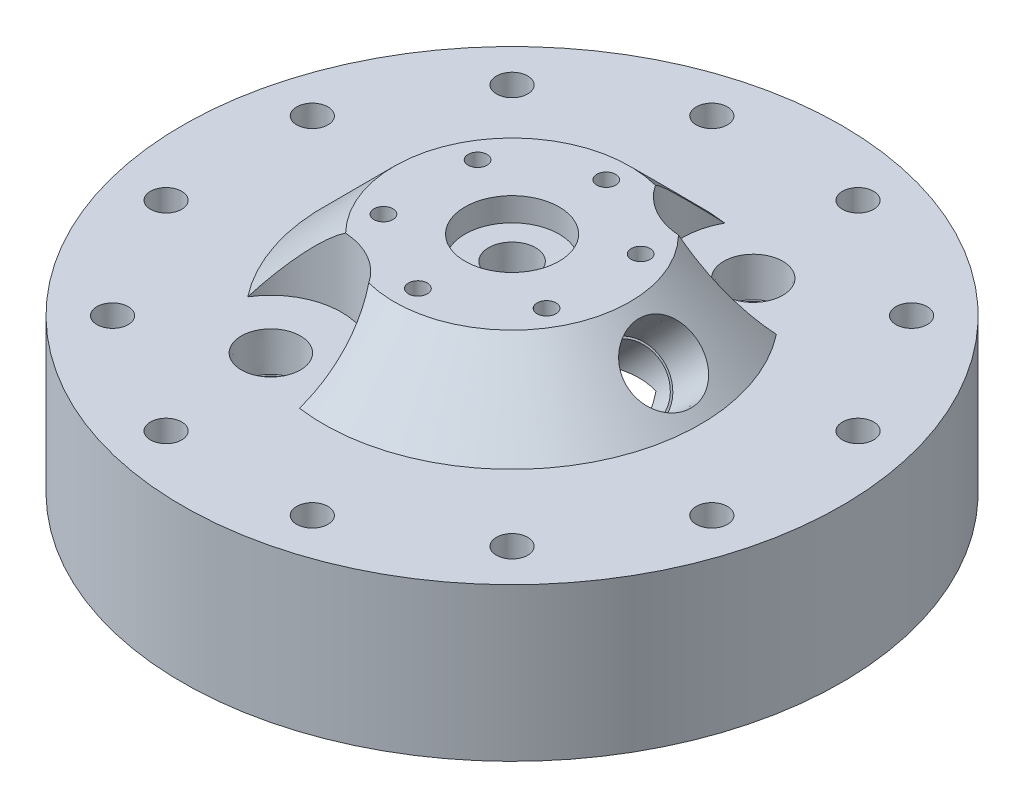
SolidWorks part; units mm, degrees
ref_plane "Front Plane" through (0, 0, 0) normal (0, 0, 1) x (1, 0, 0)
ref_plane "Top Plane" through (0, 0, 0) normal (0, 1, 0) x (1, 0, 0)
ref_plane "Right Plane" through (0, 0, 0) normal (1, 0, 0) x (0, 0, -1)
sketch "Sketch1" plane through (0, 0, 0) normal (0, 0, 1) x (1, 0, 0)
  line L0 (0, 0) -> (0, 51.199) construction
  line L2 (-88.9, 0) -> (-88.9, 41.275)
  line L3 (-88.9, 41.275) -> (-50.8, 41.275)
  line L4 (-50.8, 41.275) -> (-31.75, 60.325)
  line L5 (-31.75, 60.325) -> (-12.7, 60.325)
  line L6 (0, 53.975) -> (0, 34.925)
  line L8 (-31.75, 34.925) -> (0, 34.925)
  line L12 (-31.75, 34.925) -> (-31.75, 22.225)
  line L15 (-31.75, 22.225) -> (-50.8, 22.225)
  line L16 (-50.8, 22.225) -> (-50.8, 3.175)
  line L17 (-50.8, 3.175) -> (-52.3875, 3.175)
  line L18 (-52.3875, 3.175) -> (-52.3875, 5.715)
  line L19 (-52.3875, 5.715) -> (-55.9435, 5.715)
  line L20 (-55.9435, 5.715) -> (-55.9435, 3.175)
  line L21 (-88.9, 0) -> (-57.15, 0)
  line L23 (-55.9435, 3.175) -> (-57.15, 3.175)
  line L24 (-57.15, 3.175) -> (-57.15, 0)
  line L25 (-12.7, 60.325) -> (-12.7, 53.975)
  line L26 (-12.7, 53.975) -> (0, 53.975)
  point P8 (0, 56.7401)
  dimension "D1" = 6.35
  dimension "D2" = 31.75
  dimension "D3" = 19.05
  dimension "D4" = 31.75
  dimension "D5" = 88.9
  dimension "D6" = 12.7
  dimension "D7" = 135
  dimension "D8" = 3.175
  dimension "D9" = 22.225
  dimension "D10" = 41.275
  dimension "D11" = 6.35
  dimension "D12" = 50.8
  dimension "D13" = 3.556
  dimension "D14" = 2.54
  dimension "D15" = 1.5875
  dimension "D16" = 6.35
  dimension "D17" = 12.7
revolve "Revolve1" add sketch "Sketch1" angle 360 about L0
hole_wizard "5/16 Clearance Hole1" positions "Sketch4" profile "Sketch6" hole size "5/16" standard "ANSI Inch" end condition through all
sketch "Sketch4" plane through (0, 41.275, 0) normal (0, 1, 0) x (1, 0, 0)
  line L0 (-73.6035, -19.722) -> (0, 0) construction
  line L2 (0, 0) -> (-63.9148, 0) construction
  point P0 (-73.6035, -19.722)
  dimension "D1" = 76.2
  dimension "D2" = 15
sketch "Sketch6" plane through (-73.6035, 41.275, 19.722) normal (1, 0, 0) x (0, 0, 1)
  line L0 (0, 0) -> (0, 41.275)
  line L1 (0, 41.275) -> (4.2164, 41.275)
  line L2 (4.2164, 41.275) -> (4.2164, 0)
  line L5 (4.2164, 0) -> (0, 0)
  line L11 (0, -6.35) -> (0, 107.95) construction
  dimension "Thru Hole Dia." = 8.4328
  dimension "Thru Hole Depth" = 41.275
pattern_circular "CirPattern1" count 12 over 360 about axis through (0, 0, 0) along (0, 1, 0) of "5/16 Clearance Hole1"
hole_wizard "1/2 (0.5) Diameter Hole1" positions "Sketch7" profile "Sketch8" hole size "1/2" standard "ANSI Inch" end condition through all
sketch "Sketch7" plane through (0, 60.325, 0) normal (0, 1, 0) x (1, 0, 0)
  point P0 (0, 0)
sketch "Sketch8" plane through (0, 60.325, 0) normal (1, 0, 0) x (0, 0, 1)
  line L0 (0, 0) -> (0, 60.325)
  line L1 (0, 60.325) -> (6.35, 60.325)
  line L2 (6.35, 60.325) -> (6.35, 0)
  line L5 (6.35, 0) -> (0, 0)
  line L11 (0, -6.35) -> (0, 107.95) construction
  dimension "Thru Hole Dia." = 12.7
  dimension "Thru Hole Depth" = 60.325
ref_plane "Plane1" through (46.0375, 46.0375, 0) normal (0.7071, 0.7071, 0) x (0, 0, -1)
sketch "Sketch9" plane through (46.0375, 46.0375, 0) normal (0.7071, 0.7071, 0) x (0, 0, -1)
  line L0 (0, -6.7352) -> (0, 20.2056) construction
  ellipse E0 centre (0, 29.1858) end of major axis (-50.8, 29.1858) minor radius 35.921 construction
  ellipse E1 centre (0, 42.6562) end of major axis (-31.75, 42.6562) minor radius 22.4506 construction
  point P15 (0, 6.7352)
hole_wizard "1/2 NPT Tapped Hole1" positions "Sketch10" profile "Sketch11" size "1/2" standard "ANSI Inch" end condition through all
sketch "Sketch10" plane through (46.0375, 46.0375, 0) normal (0.7071, 0.7071, 0) x (0, 0, -1)
  point P0 (0, 6.7352)
sketch "Sketch11" plane through (41.275, 50.8, 0) normal (0, 0, 1) x (-0.7071, 0.7071, 0)
  line L0 (0, 0) -> (0, 127.9686)
  line L1 (0, 127.9686) -> (8.9281, 127.9686)
  line L2 (-9.4797, 13.462) -> (-9.8828, 0) construction
  line L3 (8.9281, 127.9686) -> (8.9281, 13.462)
  line L4 (8.9281, 13.462) -> (9.4797, 13.462)
  line L5 (9.4797, 13.462) -> (9.8828, 0)
  line L7 (9.8828, 0) -> (0, 0)
  line L8 (0, -6.35) -> (0, 107.95) construction
  line L11 (-8.9281, 13.462) -> (-9.4797, 13.462) construction
  dimension "Thru Tap Drill Dia." = 17.8562
  dimension "Thru Tap Drill Depth" = 127.9686
  dimension "Thread Dia." = 19.7656
  dimension "Thread Angle" = 3.43
  dimension "Thread Depth" = 13.462
cosmetic thread "Hole Thread3" parameters "D1"=13.462, "D2"=36.8399
hole_wizard "1 (1.5) Diameter Hole1" positions "Sketch14" profile "Sketch16" hole size "1" standard "ANSI Inch"
sketch "Sketch14" plane through (0, 60.325, 0) normal (0, 1, 0) x (1, 0, 0)
  line L0 (-23.8125, -41.2445) -> (0, 0) construction
  line L2 (0, 0) -> (-62.2091, 0) construction
  point P0 (-23.8125, -41.2445)
  dimension "D1" = 47.625
  dimension "D2" = 60
sketch "Sketch16" plane through (-23.8125, 60.325, 41.2445) normal (1, 0, 0) x (0, 0, 1)
  line L0 (0, 0) -> (0, 30.4964)
  line L1 (0, 30.4964) -> (19.05, 19.05)
  line L2 (19.05, 19.05) -> (19.05, 0)
  line L5 (19.05, 0) -> (0, 0)
  line L10 (0, 30.4964) -> (-19.05, 19.05) construction
  line L11 (0, -6.35) -> (0, 107.95) construction
  dimension "Hole Dia." = 38.1
  dimension "Hole Depth" = 19.05
  dimension "Drill Angle" = 118
hole_wizard "3/8 NPT Tapped Hole1" positions "Sketch17" profile "Sketch19" size "3/8" standard "ANSI Inch"
sketch "Sketch17" plane through (0, 41.275, 0) normal (0, 1, 0) x (1, 0, 0)
  line L0 (0, 0) -> (-55.2485, 0) construction
  line L2 (0, 0) -> (-23.8125, -41.2445) construction
  point P0 (-23.8125, -41.2445)
  dimension "D1" = 47.625
  dimension "D2" = 60
cosmetic thread "Hole Thread4" parameters "D1"=10.414, "D2"=17.1495
sketch "Sketch19" plane through (-23.8125, 41.275, 41.2445) normal (1, 0, 0) x (0, 0, 1)
  line L0 (0, 0) -> (0, 26.6406)
  line L1 (7.1374, 22.352) -> (0, 26.6406)
  line L2 (-7.1374, 22.352) -> (0, 26.6406) construction
  line L3 (7.1374, 22.352) -> (7.1374, 10.414)
  line L4 (7.1374, 10.414) -> (7.6537, 10.414)
  line L5 (7.6537, 10.414) -> (7.9655, 0)
  line L6 (-7.6537, 10.414) -> (-7.9655, 0) construction
  line L7 (7.9655, 0) -> (0, 0)
  line L8 (0, -6.35) -> (0, 107.95) construction
  line L11 (-7.1374, 10.414) -> (-7.6537, 10.414) construction
  dimension "Tap Drill Dia." = 14.2748
  dimension "Tap Drill Depth" = 22.352
  dimension "Thread Dia." = 15.9311
  dimension "Thread Angle" = 3.43
  dimension "Thread Depth" = 10.414
  dimension "Drill Angle" = 118
hole_wizard "Tap Drill for 1/4-20 Tap1" positions "Sketch20" profile "Sketch21" hole size "1/4-20" standard "ANSI Inch"
sketch "Sketch20" plane through (0, 60.325, 0) normal (0, 1, 0) x (1, 0, 0)
  line L0 (0, 0) -> (21.997, 12.7) construction
  line L2 (0, 0) -> (14.3987, 0) construction
  point P0 (21.997, 12.7)
  dimension "D1" = 25.4
  dimension "D2" = 30
sketch "Sketch21" plane through (21.997, 60.325, -12.7) normal (1, 0, 0) x (0, 0, 1)
  line L0 (0, 0) -> (0, 17.5358)
  line L1 (0, 17.5358) -> (2.5527, 16.002)
  line L2 (2.5527, 16.002) -> (2.5527, 0)
  line L5 (2.5527, 0) -> (0, 0)
  line L10 (0, 17.5358) -> (-2.5527, 16.002) construction
  line L11 (0, -6.35) -> (0, 107.95) construction
  dimension "Hole Dia." = 5.1054
  dimension "Hole Depth" = 16.002
  dimension "Drill Angle" = 118
pattern_circular "CirPattern2" count 6 over 360 about axis through (0, 0, 0) along (0, 1, 0) of "Tap Drill for 1/4-20 Tap1"
pattern_circular "CirPattern3" count 2 over 360 about axis through (0, 0, 0) along (0, 1, 0) of "1 (1.5) Diameter Hole1", "3/8 NPT Tapped Hole1"
cosmetic thread "Hole Thread5" parameters "D1"=10.414, "D2"=17.1495
hole_wizard "1/8 (0.125) Diameter Hole1" positions "Sketch22" profile "Sketch24" hole size "1/8" standard "ANSI Inch"
sketch "Sketch22" plane through (0, 22.225, 0) normal (0, -1, 0) x (-1, 0, 0)
  line L0 (0, 0) -> (-23.8125, 41.2445) construction
  line L2 (0, 0) -> (0, 44.45) construction
  point P0 (0, 44.45)
  dimension "D1" = 30
  dimension "D2" = 44.45
sketch "Sketch24" plane through (0, 22.225, -44.45) normal (1, 0, 0) x (0, 0, -1)
  line L0 (0, 0) -> (0, 7.3039)
  line L1 (0, 7.3039) -> (1.5875, 6.35)
  line L2 (1.5875, 6.35) -> (1.5875, 0)
  line L5 (1.5875, 0) -> (0, 0)
  line L10 (0, 7.3039) -> (-1.5875, 6.35) construction
  line L11 (0, -6.35) -> (0, 107.95) construction
  dimension "Hole Dia." = 3.175
  dimension "Hole Depth" = 6.35
  dimension "Drill Angle" = 118
